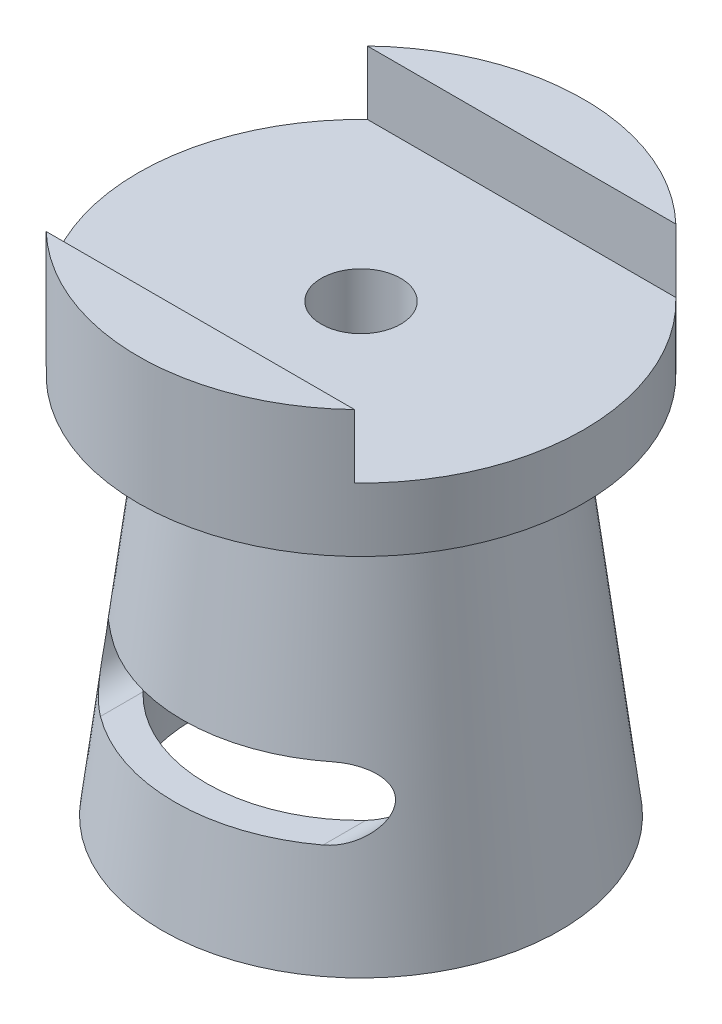
SolidWorks part; units mm, degrees
ref_plane "Front Plane" through (0, 0, 0) normal (0, 0, 1) x (1, 0, 0)
ref_plane "Top Plane" through (0, 0, 0) normal (0, 1, 0) x (1, 0, 0)
ref_plane "Right Plane" through (0, 0, 0) normal (1, 0, 0) x (0, 0, -1)
sketch "Sketch1" plane through (0, 0, 0) normal (0, 0, 1) x (1, 0, 0)
  line L0 (0, 10) -> (3.9, 10)
  line L1 (3.9, 10) -> (5.1278, 0)
  line L4 (0, 11) -> (4.7847, 11)
  line L5 (4.7847, 11) -> (6.2581, -1)
  line L6 (6.2581, -1) -> (5.2506, -1)
  line L8 (-1, -1) -> (-1, 11) construction
  line L9 (0, 0) -> (0, 10) construction
  line L10 (-1, 11) -> (4.7847, 11) construction
  line L11 (0, 0) -> (0, 10) construction
  line L12 (0, 10) -> (0, 11)
  line L13 (5.1278, 0) -> (5.2506, -1)
  line L15 (5.1278, 0) -> (0, 0) construction
  line L16 (6.2581, -1) -> (-1, -1) construction
  dimension "D1" = 3.9
  dimension "D3" = 97
  dimension "D4" = 1
revolve "Revolve1" add sketch "Sketch1" angle 360 about L12
sketch "Sketch3" plane through (0, 11, 0) normal (0, 1, 0) x (1, 0, 0)
  circle A1 centre (0, 0) radius 7
  dimension "D1" = 14
extrude "Boss-Extrude1" add sketch "Sketch3" along normal blind 4
sketch "Sketch5" plane through (0, 15, 0) normal (0, 1, 0) x (1, 0, 0)
  line L0 (-7.8165, 0) -> (7.7023, 0) construction
  line L1 (-4.8474, 5.05) -> (4.8474, 5.05)
  line L2 (-4.8474, -5.05) -> (4.8474, -5.05)
  circle A0 centre (0, 0) radius 7 construction
  arc A1 (-4.8474, 5.05) -> (-4.8474, -5.05) centre (0, 0) ccw
  arc A2 (4.8474, -5.05) -> (4.8474, 5.05) centre (0, 0) ccw
  dimension "D1" = 10.1
extrude "Cut-Extrude1" cut sketch "Sketch5" against normal blind 2
sketch "Sketch7" plane through (0, 13, 0) normal (0, 1, 0) x (1, 0, 0)
  circle A0 centre (0, 0) radius 1.25
  dimension "D1" = 2.5
extrude "Cut-Extrude2" cut sketch "Sketch7" against normal blind 3
sketch "Sketch8" plane through (0, 0, 0) normal (0, 0, 1) x (1, 0, 0)
  line L0 (-3.5, 3.3422) -> (3.5, 3.3422) construction
  line L1 (-3.5, 4.3922) -> (3.5, 4.3922)
  line L2 (-3.5, 2.2922) -> (3.5, 2.2922)
  line L3 (0, -5.2755) -> (0, 16.6823) construction
  arc A0 (-3.5, 4.3922) -> (-3.5, 2.2922) centre (-3.5, 3.3422) ccw
  arc A1 (3.5, 2.2922) -> (3.5, 4.3922) centre (3.5, 3.3422) ccw
  point P2 (0, 3.3422)
  dimension "D1" = 7
  dimension "D2" = 2.1
extrude "Cut-Extrude3" cut sketch "Sketch8" along normal blind 10
